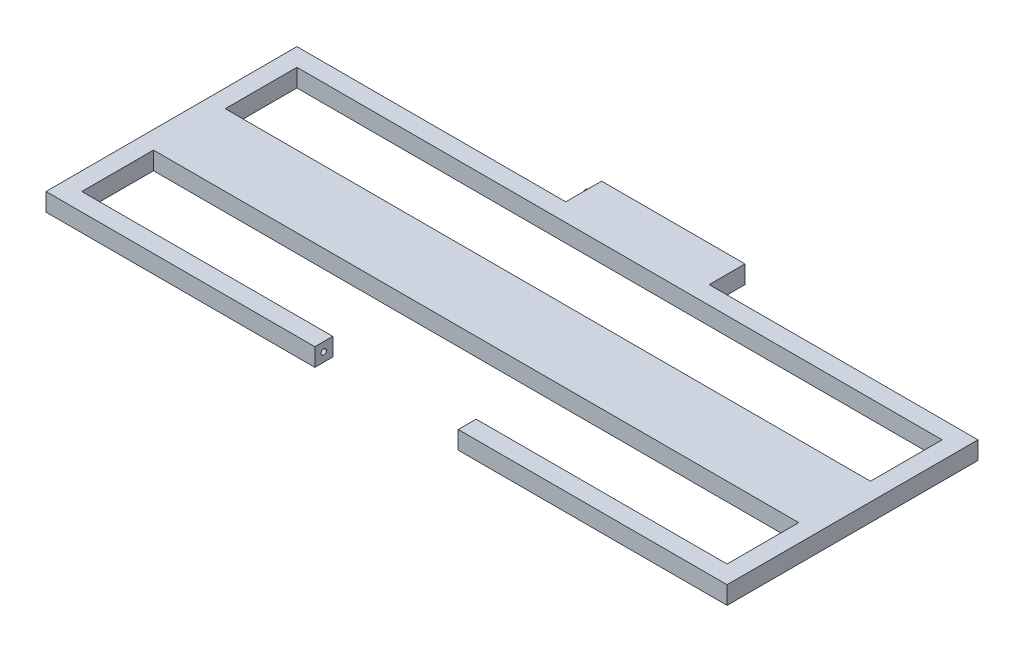
SolidWorks part; units mm, degrees
ref_plane "Alzado" through (0, 0, 0) normal (0, 0, 1) x (1, 0, 0)
ref_plane "Planta" through (0, 0, 0) normal (0, 1, 0) x (1, 0, 0)
ref_plane "Vista lateral" through (0, 0, 0) normal (1, 0, 0) x (0, 0, -1)
sketch "Croquis1" plane through (0, 0, 0) normal (0, 1, 0) x (1, 0, 0)
  line L0 (-450, 425) -> (450, 425)
  line L1 (-475, -600) -> (-100, -600)
  line L2 (-475, -600) -> (-475, 600)
  line L3 (-475, 600) -> (475, 600)
  line L4 (475, -600) -> (475, 600)
  line L5 (-475, -600) -> (475, 600) construction
  line L6 (-475, 600) -> (475, -600) construction
  line L7 (-450, -575) -> (-100, -575)
  line L8 (-450, -575) -> (-450, 575)
  line L9 (-450, 575) -> (450, 575)
  line L10 (450, -575) -> (450, 575)
  line L11 (-450, -575) -> (450, 575) construction
  line L12 (-450, 575) -> (450, -575) construction
  line L13 (-450, 275) -> (450, 275)
  line L14 (-450, 125) -> (450, 125)
  line L15 (-450, -25) -> (450, -25)
  line L16 (-450, -175) -> (450, -175)
  line L17 (-178.125, -225) -> (-176.087, -225)
  line L18 (-450, -375) -> (450, -375)
  line L19 (176.087, -225) -> (178.125, -225)
  line L20 (-450, -475) -> (450, -475)
  line L21 (-450, 575) -> (-450, 425) construction
  line L22 (-100, -600) -> (-100, -575)
  line L23 (100, -600) -> (100, -575)
  line L24 (100, -600) -> (475, -600)
  line L25 (100, -575) -> (450, -575)
  line L26 (-450, -275) -> (450, -275)
  line L27 (-257.2917, -325) -> (-254.3478, -325) [skipped]
  line L28 (-100, -575) -> (100, -575)
  point P0 (0, 0)
  point P6 (0, 0)
  dimension "D1" = 950
  dimension "D2" = 1200
  dimension "D3" = 900
  dimension "D4" = 1150
  dimension "D6" = 150
  dimension "D7" = 375
  dimension "D8" = 200
  dimension "D9" = 100
  dimension "D10" = 100
  dimension "D5" = 8
extrude "Saliente-Extruir2" add sketch "Croquis1" along normal blind 25
sketch "Croquis2" plane through (-100, 0, 0) normal (1, 0, 0) x (0, 0, -1)
  line L0 (-600, 25) -> (-575, 0)
  circle A0 centre (-587.5, 12.5) radius 3.75
  dimension "D1" = 7.5
extrude "Cortar-Extruir1" cut sketch "Croquis2" against normal blind 10 contours L0 A0 | L0 A0
sketch "Croquis3" plane through (0, 0, -600) normal (0, 0, -1) x (-1, 0, 0)
  line L1 (-475, 0) -> (475, 0)
  line L2 (-475, 0) -> (-475, 25)
  line L3 (-475, 25) -> (475, 25)
  line L4 (475, 0) -> (475, 25)
extrude "Cortar-Extruir2" cut sketch "Croquis3" against normal blind 850
sketch "Croquis4" plane through (0, 0, 250) normal (0, 0, -1) x (-1, 0, 0)
  line L0 (0, 0) -> (0, 25) construction
  line L1 (475, 25) -> (-475, 25) construction
  line L3 (-100, 0) -> (100, 0)
  line L4 (-100, 0) -> (-100, 25)
  line L5 (-100, 25) -> (100, 25)
  line L6 (100, 0) -> (100, 25)
  line L7 (-100, 0) -> (100, 25) construction
  line L8 (-100, 25) -> (100, 0) construction
  point P5 (0, 12.5)
  dimension "D1" = 200
extrude "Saliente-Extruir3" add sketch "Croquis4" along normal blind 50
sketch "Croquis5" plane through (-100, 0, 0) normal (-1, 0, 0) x (0, 0, 1)
  line L0 (225, 25) -> (225, 0) construction
  line L1 (200, 25) -> (250, 25) construction
  line L2 (200, 0) -> (250, 0) construction
  line L3 (200, 0) -> (200, 25) construction
  line L4 (225, 0) -> (200, 25) construction
  circle A0 centre (212.5, 12.5) radius 3.75
  dimension "D2" = 7.5
  dimension "D1" = 25
extrude "Saliente-Extruir4" add sketch "Croquis5" along normal blind 10
